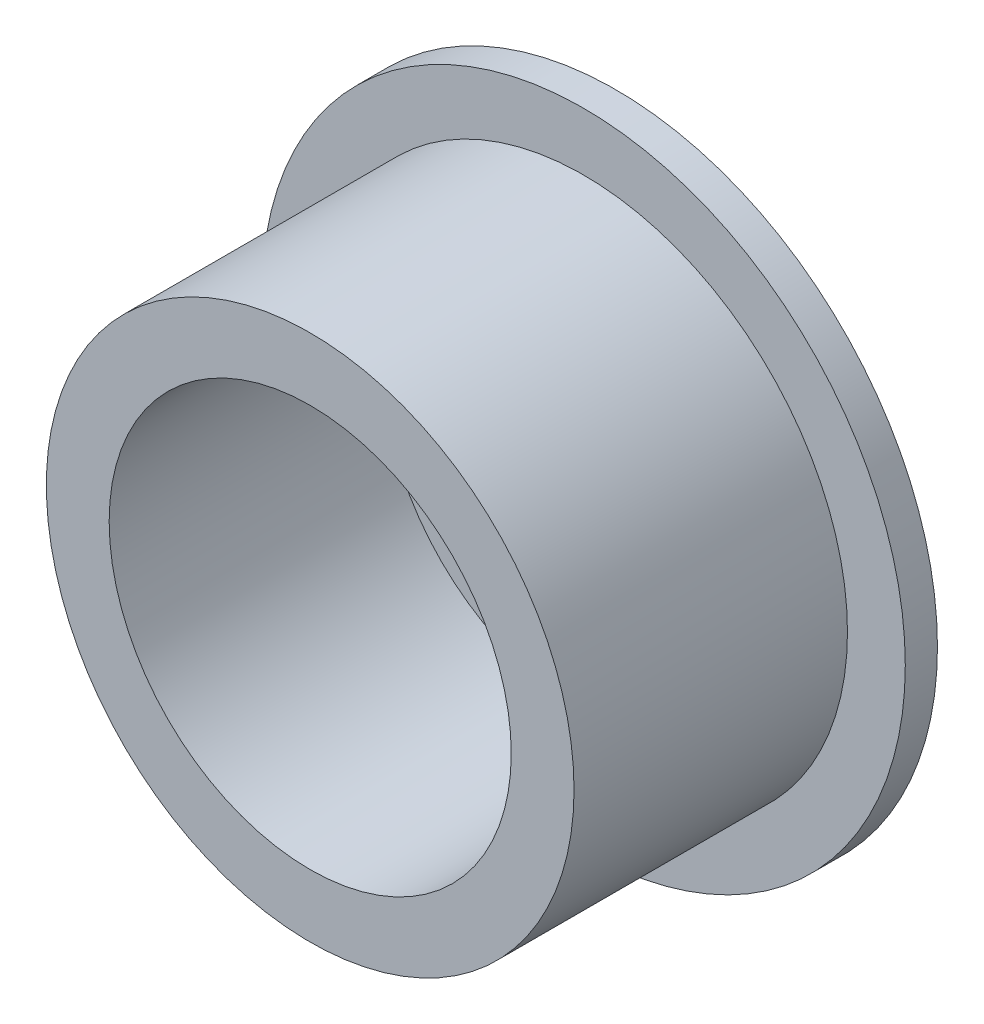
SolidWorks part; units mm, degrees
ref_plane "Front Plane" through (0, 0, 0) normal (0, 0, 1) x (1, 0, 0)
ref_plane "Top Plane" through (0, 0, 0) normal (0, 1, 0) x (1, 0, 0)
ref_plane "Right Plane" through (0, 0, 0) normal (1, 0, 0) x (0, 0, -1)
sketch "Sketch1" plane through (0, 0, 0) normal (0, 0, 1) x (1, 0, 0)
  line L0 (0, 0) -> (0, 20) construction
  line L1 (0, 0) -> (0, 10) construction
  circle A0 centre (0, 0) radius 20
  circle A1 centre (0, 10) radius 1.5
  circle A3 centre (10, 0) radius 1.5
  circle A4 centre (0, -10) radius 1.5
  circle A5 centre (-10, 0) radius 1.5
  dimension "D1" = 40
  dimension "D3" = 3
  dimension "D2" = 10
  dimension "D4" = 10
  dimension "D5" = 10
extrude "Boss-Extrude1" add sketch "Sketch1" along normal blind 2
sketch "Sketch2" plane through (0, 0, 2) normal (0, 0, 1) x (1, 0, 0)
  circle A0 centre (0, 0) radius 16.405
  circle A1 centre (0, 0) radius 12.5
  dimension "D1" = 32.81
  dimension "D2" = 25
extrude "Boss-Extrude2" add sketch "Sketch2" along normal blind 17
sketch "Sketch4" plane through (0, 0, 0) normal (0, 0, -1) x (-1, 0, 0)
  circle A0 centre (0, 0) radius 7.62
  dimension "D1" = 15.24
extrude "Cut-Extrude1" cut sketch "Sketch4" against normal blind 17
